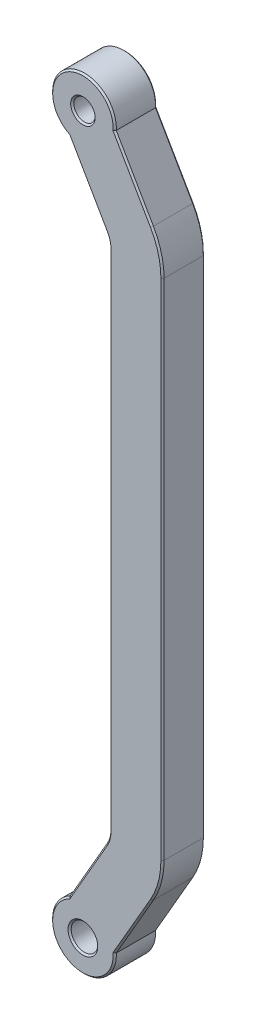
SolidWorks part; units mm, degrees
material "POM 乙缩醛共聚物"
ref_plane "前视基准面" through (0, 0, 0) normal (0, 0, 1) x (1, 0, 0)
ref_plane "上视基准面" through (0, 0, 0) normal (0, 1, 0) x (1, 0, 0)
ref_plane "右视基准面" through (0, 0, 0) normal (1, 0, 0) x (0, 0, -1)
sketch "草图1" plane through (0, 0, 0) normal (0, 0, 1) x (1, 0, 0)
  line L0 (0, 0) -> (0, 135) construction
  circle A0 centre (0, 0) radius 6
  circle A1 centre (0, 135) radius 6
  dimension "D2" = 12
  dimension "D1" = 135
extrude "凸台-拉伸1" add sketch "草图1" along normal blind 8
sketch "草图2" plane through (0, 0, 0) normal (0, 0, 1) x (1, 0, 0)
  line L0 (0, 135) -> (0, 0) construction
  line L1 (0, 135) -> (10, 117.6795)
  line L2 (10, 117.6795) -> (10, 17.3205)
  line L3 (10, 17.3205) -> (0, 0)
  line L4 (0, 67.5) -> (10, 67.5) construction
  dimension "D1" = 10
  dimension "D2" = 30
extrude "拉伸-薄壁1" add sketch "草图2" along normal up to surface (8 mm away) thin up to face at (6, 135, 8) thin type mid plane wall 10
sketch "草图3" plane through (0, 0, 8) normal (0, 0, 1) x (1, 0, 0)
  circle A1 centre (0, 0) radius 2.5
  dimension "D1" = 5
extrude "切除-拉伸1" cut sketch "草图3" against normal through all
sketch "草图4" plane through (0, 0, 0) normal (0, 0, -1) x (-1, 0, 0)
  circle A0 centre (0, 135) radius 2
  dimension "D1" = 4
extrude "切除-拉伸2" cut sketch "草图4" against normal through all
sketch "草图5" plane through (0, 0, 0) normal (0, 0, -1) x (-1, 0, 0)
  circle A0 centre (0, 135) radius 4
  dimension "D1" = 8
extrude "切除-拉伸3" cut sketch "草图5" against normal blind 4.5
chamfer "倒角1" distance 0.3 angle 45 28 edges at (4.8296, 116.2941, 8) (4.8296, 116.2941, 0) (5, 67.5, 8) (5, 67.5, 0) (4.8296, 18.7059, 8) (4.8296, 18.7059, 0) (0.8292, 11.4361, 0) (0.8292, 11.4361, 8) (-3, -5.1962, 0) (9.4894, 6.4361, 0) (9.4894, 6.4361, 8) (14.4889, 16.1177, 8) (14.4889, 16.1177, 0) (15, 67.5, 8) (15, 67.5, 0) (14.4889, 118.8823, 8) (14.4889, 118.8823, 0) (9.4894, 128.5639, 0) (9.4894, 128.5639, 8) (-3, 140.1962, 0) (0.8292, 123.5639, 0) (0.8292, 123.5639, 8) (2.5, 0, 0) (-4, 135, 0) (-3, -5.1962, 8) (-3, 140.1962, 8) (2.5, 0, 8) (-2, 135, 8)
